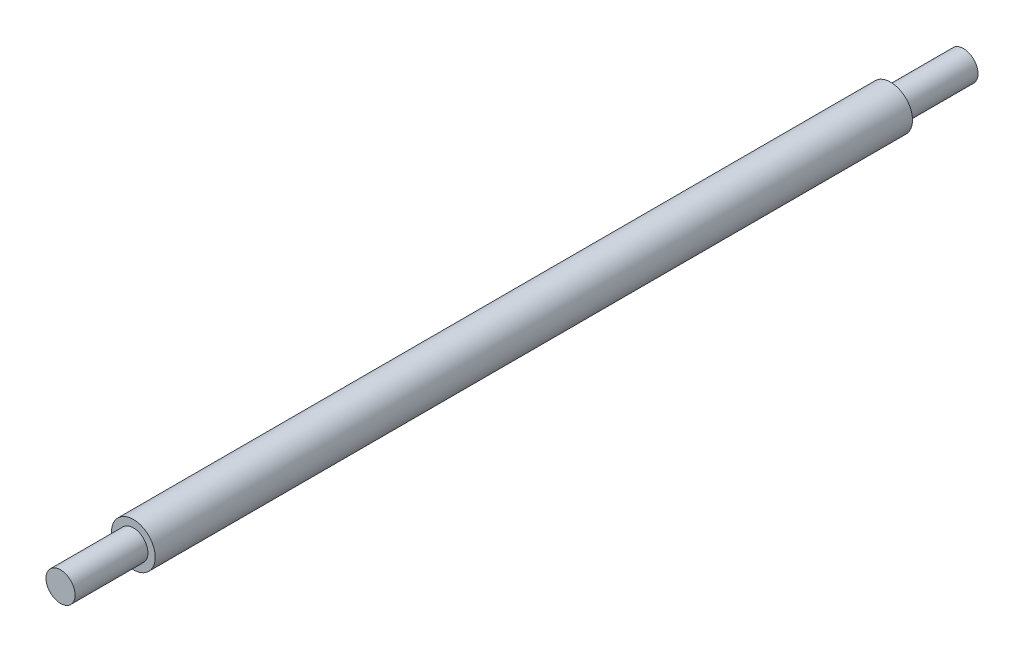
SolidWorks part; units mm, degrees
ref_plane "Front Plane" through (0, 0, 0) normal (0, 0, 1) x (1, 0, 0)
ref_plane "Top Plane" through (0, 0, 0) normal (0, 1, 0) x (1, 0, 0)
ref_plane "Right Plane" through (0, 0, 0) normal (1, 0, 0) x (0, 0, -1)
sketch "Sketch1" plane through (0, 0, 0) normal (0, 0, 1) x (1, 0, 0)
  circle A0 centre (0, 0) radius 3
  dimension "D1" = 6
extrude "Boss-Extrude1" add sketch "Sketch1" along normal mid plane 104
sketch "Sketch2" plane through (0, 0, 52) normal (0, 0, 1) x (1, 0, 0)
  circle A0 centre (0, 0) radius 2
  dimension "D1" = 4
extrude "Boss-Extrude2" add sketch "Sketch2" along normal blind 10
sketch "Sketch3" plane through (0, 0, -52) normal (0, 0, -1) x (-1, 0, 0)
  circle A0 centre (0, 0) radius 2
  dimension "D1" = 4
extrude "Boss-Extrude3" add sketch "Sketch3" along normal blind 10
